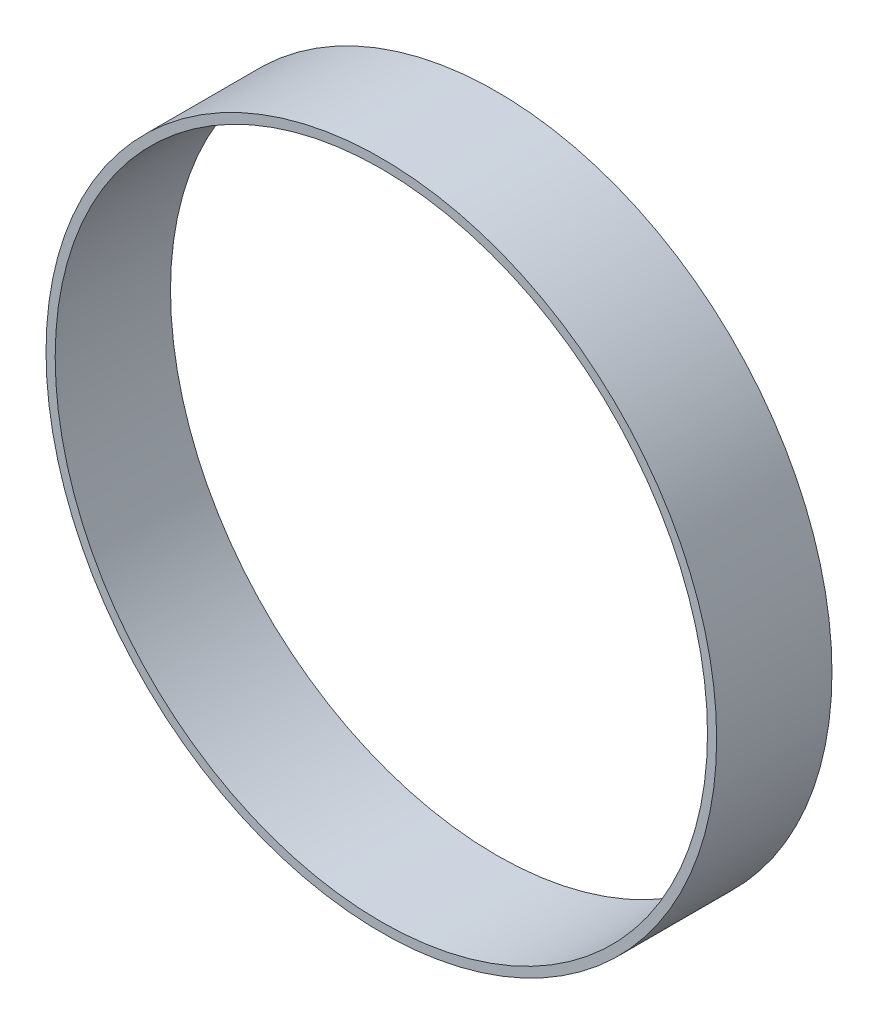
SolidWorks part; units mm, degrees
material "EPDM 60 Durometer"
ref_plane "Front Plane" through (0, 0, 0) normal (0, 0, 1) x (1, 0, 0)
ref_plane "Top Plane" through (0, 0, 0) normal (0, 1, 0) x (1, 0, 0)
ref_plane "Right Plane" through (0, 0, 0) normal (1, 0, 0) x (0, 0, -1)
sketch "Sketch1" plane through (0, 0, 0) normal (0, 0, 1) x (1, 0, 0)
  circle A0 centre (0, 0) radius 29.075
  circle A1 centre (0, 0) radius 28.2812
  dimension "D1" = 58.15
  dimension "D2" = 0.7937
extrude "Boss-Extrude1" add sketch "Sketch1" along normal mid plane 10 contours A0 | A1
